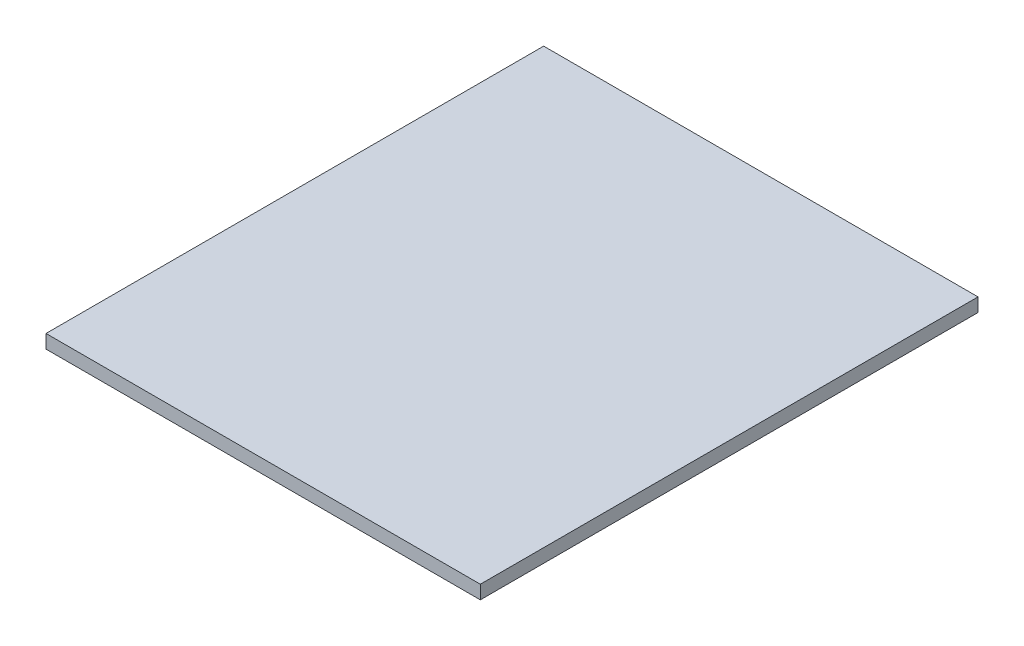
SolidWorks part; units mm, degrees
ref_plane "Ebene vorne" through (0, 0, 0) normal (0, 0, 1) x (1, 0, 0)
ref_plane "Ebene oben" through (0, 0, 0) normal (0, 1, 0) x (1, 0, 0)
ref_plane "Ebene rechts" through (0, 0, 0) normal (1, 0, 0) x (0, 0, -1)
sketch "Skizze1" plane through (0, 0, 0) normal (0, 1, 0) x (1, 0, 0)
  line L1 (0, 0) -> (192, 0)
  line L2 (0, 0) -> (0, 220)
  line L3 (0, 220) -> (192, 220)
  line L4 (192, 0) -> (192, 220)
  dimension "D1" = 192
  dimension "D2" = 220
extrude "Aufsatz-Linear austragen1" add sketch "Skizze1" along normal blind 6
